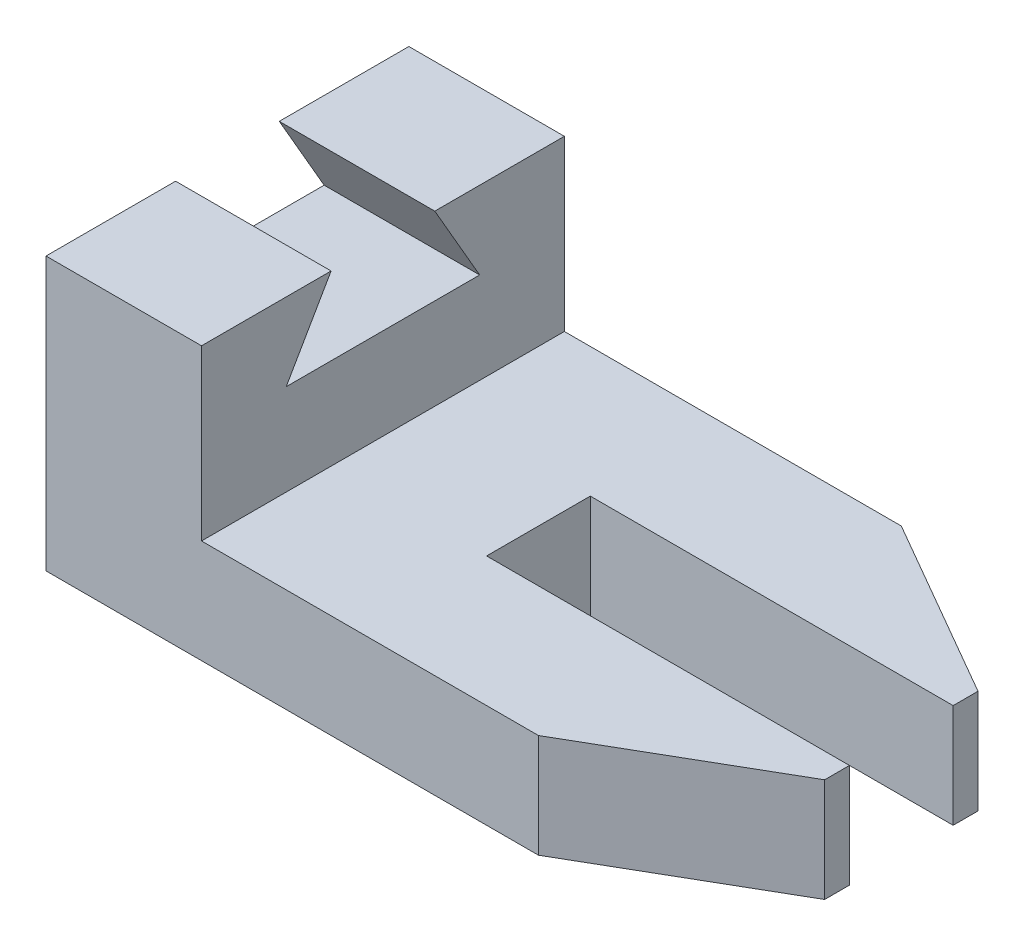
SolidWorks part; units mm, degrees
ref_plane "Alzado" through (0, 0, 0) normal (0, 0, 1) x (1, 0, 0)
ref_plane "Planta" through (0, 0, 0) normal (0, 1, 0) x (1, 0, 0)
ref_plane "Vista lateral" through (0, 0, 0) normal (1, 0, 0) x (0, 0, -1)
sketch "Croquis2" plane through (0, 0, 0) normal (0, 1, 0) x (1, 0, 0)
  line L0 (130, 20.2073) -> (130, 24.9973)
  line L1 (0, 0) -> (95, 0)
  line L2 (0, 0) -> (0, 70)
  line L3 (0, 70) -> (95, 70)
  line L4 (130, 44.9973) -> (130, 49.7927)
  line L5 (95, 70) -> (130, 49.7927)
  line L6 (95, 0) -> (130, 20.2073)
  line L10 (130, 24.9973) -> (60, 24.9973)
  line L11 (60, 24.9973) -> (60, 44.9973)
  line L12 (60, 44.9973) -> (130, 44.9973)
  dimension "D1" = 70
  dimension "D2" = 35
  dimension "D3" = 95
  dimension "D4" = 4.79
  dimension "D5" = 20.2073
  dimension "D6" = 20
  dimension "D7" = 70
extrude "Saliente-Extruir4" add sketch "Croquis2" along normal blind 20
sketch "Croquis4" plane through (0, 0, 0) normal (-1, 0, 0) x (0, 0, 1)
  line L0 (-35, 0) -> (-35, 52.6092) construction
  line L1 (-70, 0) -> (0, 0) construction
  line L2 (0, 20) -> (0, 52.6092)
  line L3 (0, 52.6092) -> (-25, 52.6092)
  line L4 (-25, 52.6092) -> (-16.3397, 37.6092)
  line L5 (-16.3397, 37.6092) -> (-35, 37.6092)
  line L6 (-35, 37.6092) -> (-35, 20)
  line L7 (-35, 20) -> (0, 20)
  point P15 (-35, 37.6092)
  dimension "D1" = 60
  dimension "D2" = 15
extrude "Saliente-Extruir5" add sketch "Croquis4" against normal blind 30
ref_plane "Plano1" through (0, 0, -35) normal (0, 0, -1) x (-1, 0, 0)
mirror "Simetría1" about plane through (0, 0, -35) normal (0, 0, -1) of "Saliente-Extruir5"
